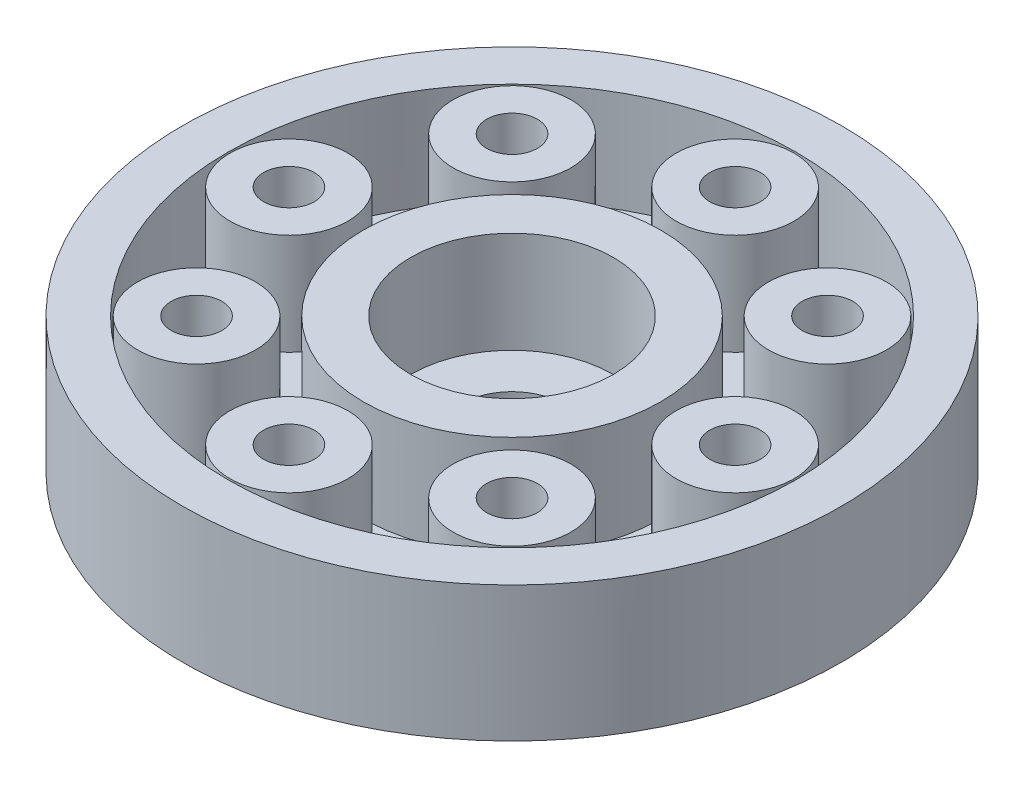
SolidWorks part; units mm, degrees
ref_plane "前视基准面" through (0, 0, 0) normal (0, 0, 1) x (1, 0, 0)
ref_plane "上视基准面" through (0, 0, 0) normal (0, 1, 0) x (1, 0, 0)
ref_plane "右视基准面" through (0, 0, 0) normal (1, 0, 0) x (0, 0, -1)
sketch "草图1" plane through (0, 0, 0) normal (0, 1, 0) x (1, 0, 0)
  circle A0 centre (0.3947, -0.592) radius 9.75
  arc A1 (-0.0261, 2.2521) -> (-0.4282, 2.7466) centre (-1.4141, 1.5344) ccw
  arc A2 (0.0949, 2.2673) -> (-0.0261, 2.2521) centre (0.3947, -0.592) ccw
  arc A3 (0.3614, 2.8463) -> (0.0949, 2.2673) centre (1.6177, 1.9174) ccw
  arc A4 (0.4279, 2.8463) -> (0.3614, 2.8463) centre (0.3947, -0.592) ccw
  arc A5 (0.6944, 2.2673) -> (0.4279, 2.8463) centre (-0.8284, 1.9174) ccw
  arc A6 (0.8154, 2.2521) -> (0.6944, 2.2673) centre (0.3947, -0.592) ccw
  arc A7 (1.2175, 2.7466) -> (0.8154, 2.2521) centre (2.2034, 1.5344) ccw
  arc A8 (1.282, 2.73) -> (1.2175, 2.7466) centre (0.3947, -0.592) ccw
  arc A9 (1.3961, 2.103) -> (1.282, 2.73) centre (-0.1659, 2.1427) ccw
  arc A10 (1.5095, 2.0581) -> (1.3961, 2.103) centre (0.3947, -0.592) ccw
  arc A11 (2.0219, 2.4371) -> (1.5095, 2.0581) centre (2.6754, 1.0178) ccw
  arc A12 (2.0803, 2.405) -> (2.0219, 2.4371) centre (0.3947, -0.592) ccw
  arc A13 (2.0348, 1.7693) -> (2.0803, 2.405) centre (0.5318, 2.1962) ccw
  arc A14 (2.1335, 1.6976) -> (2.0348, 1.7693) centre (0.3947, -0.592) ccw
  arc A15 (2.7241, 1.9372) -> (2.1335, 1.6976) centre (3.004, 0.4) ccw
  arc A16 (2.7726, 1.8917) -> (2.7241, 1.9372) centre (0.3947, -0.592) ccw
  arc A17 (2.5705, 1.2872) -> (2.7726, 1.8917) centre (1.2209, 2.0745) ccw
  arc A18 (2.6483, 1.1932) -> (2.5705, 1.2872) centre (0.3947, -0.592) ccw
  arc A19 (3.2799, 1.2785) -> (2.6483, 1.1932) centre (3.1688, -0.2801) ccw
  arc A20 (3.3156, 1.2223) -> (3.2799, 1.2785) centre (0.3947, -0.592) ccw
  arc A21 (2.9695, 0.687) -> (3.3156, 1.2223) centre (1.858, 1.7853) ccw
  arc A22 (3.0214, 0.5766) -> (2.9695, 0.687) centre (0.3947, -0.592) ccw
  arc A23 (3.6544, 0.5022) -> (3.0214, 0.5766) centre (3.1592, -0.9798) ccw
  arc A24 (3.675, 0.4389) -> (3.6544, 0.5022) centre (0.3947, -0.592) ccw
  arc A25 (3.2067, 0.0065) -> (3.675, 0.4389) centre (2.4033, 1.3467) ccw
  arc A26 (3.2295, -0.1133) -> (3.2067, 0.0065) centre (0.3947, -0.592) ccw
  arc A27 (3.8241, -0.3429) -> (3.2295, -0.1133) centre (2.9759, -1.6551) ccw
  arc A28 (3.8283, -0.4093) -> (3.8241, -0.3429) centre (0.3947, -0.592) ccw
  arc A29 (3.2672, -0.7116) -> (3.8283, -0.4093) centre (2.8223, 0.7862) ccw
  arc A30 (3.2595, -0.8334) -> (3.2672, -0.7116) centre (0.3947, -0.592) ccw
  arc A31 (3.7783, -1.2036) -> (3.2595, -0.8334) centre (2.6304, -2.2636) ccw
  arc A32 (3.7659, -1.269) -> (3.7783, -1.2036) centre (0.3947, -0.592) ccw
  arc A33 (3.1472, -1.4222) -> (3.7659, -1.269) centre (3.0888, 0.1392) ccw
  arc A34 (3.1095, -1.5382) -> (3.1472, -1.4222) centre (0.3947, -0.592) ccw
  arc A35 (3.5199, -2.0259) -> (3.1095, -1.5382) centre (2.1445, -2.7671) ccw
  arc A36 (3.4916, -2.0861) -> (3.5199, -2.0259) centre (0.3947, -0.592) ccw
  arc A37 (2.8542, -2.0806) -> (3.4916, -2.0861) centre (3.186, -0.5538) ccw
  arc A38 (2.7889, -2.1837) -> (2.8542, -2.0806) centre (0.3947, -0.592) ccw
  arc A39 (3.0652, -2.758) -> (2.7889, -2.1837) centre (1.5486, -3.1339) ccw
  arc A40 (3.0227, -2.8093) -> (3.0652, -2.758) centre (0.3947, -0.592) ccw
  arc A41 (2.4068, -2.6455) -> (3.0227, -2.8093) centre (3.1078, -1.2491) ccw
  arc A42 (2.3178, -2.7291) -> (2.4068, -2.6455) centre (0.3947, -0.592) ccw
  arc A43 (2.4426, -3.3541) -> (2.3178, -2.7291) centre (0.8801, -3.341) ccw
  arc A44 (2.3887, -3.3932) -> (2.4426, -3.3541) centre (0.3947, -0.592) ccw
  arc A45 (1.8329, -3.0814) -> (2.3887, -3.3932) centre (2.8591, -1.9032) ccw
  arc A46 (1.7259, -3.1402) -> (1.8329, -3.0814) centre (0.3947, -0.592) ccw
  arc A47 (1.6913, -3.7766) -> (1.7259, -3.1402) centre (0.1812, -3.3754) ccw
  arc A48 (1.6295, -3.8011) -> (1.6913, -3.7766) centre (0.3947, -0.592) ccw
  arc A49 (1.1686, -3.3609) -> (1.6295, -3.8011) centre (2.4556, -2.4749) ccw
  arc A50 (1.0504, -3.3912) -> (1.1686, -3.3609) centre (0.3947, -0.592) ccw
  arc A51 (0.8586, -3.999) -> (1.0504, -3.3912) centre (-0.5043, -3.2349) ccw
  arc A52 (0.7926, -4.0074) -> (0.8586, -3.999) centre (0.3947, -0.592) ccw
  arc A53 (0.4557, -3.4663) -> (0.7926, -4.0074) centre (1.9226, -2.9283) ccw
  arc A54 (0.3337, -3.4663) -> (0.4557, -3.4663) centre (0.3947, -0.592) ccw
  arc A55 (-0.0033, -4.0074) -> (0.3337, -3.4663) centre (-1.1333, -2.9283) ccw
  arc A56 (-0.0693, -3.999) -> (-0.0033, -4.0074) centre (0.3947, -0.592) ccw
  arc A57 (-0.2611, -3.3912) -> (-0.0693, -3.999) centre (1.2936, -3.2349) ccw
  arc A58 (-0.3793, -3.3609) -> (-0.2611, -3.3912) centre (0.3947, -0.592) ccw
  arc A59 (-0.8401, -3.8011) -> (-0.3793, -3.3609) centre (-1.6663, -2.4749) ccw
  arc A60 (-0.902, -3.7766) -> (-0.8401, -3.8011) centre (0.3947, -0.592) ccw
  arc A61 (-0.9366, -3.1402) -> (-0.902, -3.7766) centre (0.6081, -3.3754) ccw
  arc A62 (-1.0435, -3.0814) -> (-0.9366, -3.1402) centre (0.3947, -0.592) ccw
  arc A63 (-1.5994, -3.3932) -> (-1.0435, -3.0814) centre (-2.0698, -1.9032) ccw
  arc A64 (-1.6533, -3.3541) -> (-1.5994, -3.3932) centre (0.3947, -0.592) ccw
  arc A65 (-1.5285, -2.7291) -> (-1.6533, -3.3541) centre (-0.0908, -3.341) ccw
  arc A66 (-1.6174, -2.6455) -> (-1.5285, -2.7291) centre (0.3947, -0.592) ccw
  arc A67 (-2.2334, -2.8093) -> (-1.6174, -2.6455) centre (-2.3185, -1.2491) ccw
  arc A68 (-2.2758, -2.758) -> (-2.2334, -2.8093) centre (0.3947, -0.592) ccw
  arc A69 (-1.9995, -2.1837) -> (-2.2758, -2.758) centre (-0.7592, -3.1339) ccw
  arc A70 (-2.0649, -2.0806) -> (-1.9995, -2.1837) centre (0.3947, -0.592) ccw
  arc A71 (-2.7023, -2.0861) -> (-2.0649, -2.0806) centre (-2.3967, -0.5538) ccw
  arc A72 (-2.7306, -2.0259) -> (-2.7023, -2.0861) centre (0.3947, -0.592) ccw
  arc A73 (-2.3202, -1.5382) -> (-2.7306, -2.0259) centre (-1.3551, -2.7671) ccw
  arc A74 (-2.3579, -1.4222) -> (-2.3202, -1.5382) centre (0.3947, -0.592) ccw
  arc A75 (-2.9765, -1.269) -> (-2.3579, -1.4222) centre (-2.2995, 0.1392) ccw
  arc A76 (-2.989, -1.2036) -> (-2.9765, -1.269) centre (0.3947, -0.592) ccw
  arc A77 (-2.4702, -0.8334) -> (-2.989, -1.2036) centre (-1.8411, -2.2636) ccw
  arc A78 (-2.4779, -0.7116) -> (-2.4702, -0.8334) centre (0.3947, -0.592) ccw
  arc A79 (-3.039, -0.4093) -> (-2.4779, -0.7116) centre (-2.033, 0.7862) ccw
  arc A80 (-3.0348, -0.3429) -> (-3.039, -0.4093) centre (0.3947, -0.592) ccw
  arc A81 (-2.4402, -0.1133) -> (-3.0348, -0.3429) centre (-2.1866, -1.6551) ccw
  arc A82 (-2.4173, 0.0065) -> (-2.4402, -0.1133) centre (0.3947, -0.592) ccw
  arc A83 (-2.8857, 0.4389) -> (-2.4173, 0.0065) centre (-1.6139, 1.3467) ccw
  arc A84 (-2.8651, 0.5022) -> (-2.8857, 0.4389) centre (0.3947, -0.592) ccw
  arc A85 (-2.2321, 0.5766) -> (-2.8651, 0.5022) centre (-2.3699, -0.9798) ccw
  arc A86 (-2.1802, 0.687) -> (-2.2321, 0.5766) centre (0.3947, -0.592) ccw
  arc A87 (-2.5263, 1.2223) -> (-2.1802, 0.687) centre (-1.0687, 1.7853) ccw
  arc A88 (-2.4906, 1.2785) -> (-2.5263, 1.2223) centre (0.3947, -0.592) ccw
  arc A89 (-1.859, 1.1932) -> (-2.4906, 1.2785) centre (-2.3794, -0.2801) ccw
  arc A90 (-1.7812, 1.2872) -> (-1.859, 1.1932) centre (0.3947, -0.592) ccw
  arc A91 (-1.9833, 1.8917) -> (-1.7812, 1.2872) centre (-0.4315, 2.0745) ccw
  arc A92 (-1.9348, 1.9372) -> (-1.9833, 1.8917) centre (0.3947, -0.592) ccw
  arc A93 (-1.3442, 1.6976) -> (-1.9348, 1.9372) centre (-2.2147, 0.4) ccw
  arc A94 (-1.2455, 1.7693) -> (-1.3442, 1.6976) centre (0.3947, -0.592) ccw
  arc A95 (-1.2909, 2.405) -> (-1.2455, 1.7693) centre (0.2576, 2.1962) ccw
  arc A96 (-1.2326, 2.4371) -> (-1.2909, 2.405) centre (0.3947, -0.592) ccw
  arc A97 (-0.7202, 2.0581) -> (-1.2326, 2.4371) centre (-1.886, 1.0178) ccw
  arc A98 (-0.6067, 2.103) -> (-0.7202, 2.0581) centre (0.3947, -0.592) ccw
  arc A99 (-0.4927, 2.73) -> (-0.6067, 2.103) centre (0.9553, 2.1427) ccw
  arc A100 (-0.4282, 2.7466) -> (-0.4927, 2.73) centre (0.3947, -0.592) ccw
extrude "凸台-拉伸1" add sketch "草图1" along normal blind 3
ref_plane "基准面1" through (0, 0, 0) normal (0, -1, 0) x (-1, 0, 0)
sketch "草图2" plane through (0, 0, 0) normal (0, -1, 0) x (-1, 0, 0)
  line L0 (10.4941, -0.7442) -> (4.2859, -0.7442) construction
  circle A0 centre (-0.3947, -0.592) radius 9.75
extrude "凸台-拉伸2" add sketch "草图2" along normal blind 1
ref_plane "基准面2" through (0, 0, 0) normal (0, 1, 0) x (1, 0, 0)
sketch "草图4" plane through (0, 0, 0) normal (0, 1, 0) x (1, 0, 0)
  circle A0 centre (0.3947, -0.592) radius 1.5
extrude "切除-拉伸4" cut sketch "草图4" against normal blind 1
ref_plane "基准面3" through (0, 3, 0) normal (0, 1, 0) x (1, 0, 0)
sketch "草图5" plane through (0, 0, 0) normal (0, -1, 0) x (-1, 0, 0)
  circle A0 centre (-0.3947, -0.592) radius 4.4
  circle A1 centre (-0.3947, -0.592) radius 8.4
extrude "切除-拉伸5" cut sketch "草图5" against normal blind 10
sketch "草图6" plane through (0, 0, 0) normal (0, -1, 0) x (-1, 0, 0)
  line L0 (-0.3947, -0.592) -> (-0.3947, 7.808) construction
  circle A0 centre (-0.3947, -0.592) radius 6.6 construction
  circle A1 centre (-0.3947, -0.592) radius 8.4 construction
  circle A2 centre (-0.3947, 6.008) radius 0.75
  circle A3 centre (4.2722, 4.0749) radius 0.75
  circle A4 centre (6.2053, -0.592) radius 0.75
  circle A5 centre (4.2722, -5.2589) radius 0.75
  circle A6 centre (-0.3947, -7.192) radius 0.75
  circle A7 centre (-5.0616, -5.2589) radius 0.75
  circle A8 centre (-6.9947, -0.592) radius 0.75
  circle A9 centre (-5.0616, 4.0749) radius 0.75
  circle A10 centre (-0.3947, 6.008) radius 1.7445
  circle A11 centre (4.2722, 4.0749) radius 1.7445
  circle A12 centre (6.2053, -0.592) radius 1.7445
  circle A13 centre (4.2722, -5.2589) radius 1.7445
  circle A14 centre (-0.3947, -7.192) radius 1.7445
  circle A15 centre (-5.0616, -5.2589) radius 1.7445
  circle A16 centre (-6.9947, -0.592) radius 1.7445
  circle A17 centre (-5.0616, 4.0749) radius 1.7445
  point P26 (-0.3947, -0.592)
  point P42 (-0.3947, -0.592)
  dimension "D1" = 8
  dimension "D2" = 8
extrude "凸台-拉伸3" add sketch "草图6" against normal blind 3
ref_plane "基准面4" through (0, -1, 0) normal (0, -1, 0) x (-1, 0, 0)
sketch "草图7" plane through (0, -1, 0) normal (0, -1, 0) x (-1, 0, 0)
  circle A0 centre (-0.3947, 6.008) radius 0.75 construction
  circle A1 centre (-0.3947, -0.592) radius 1.5 construction
  circle A2 centre (-0.3947, 6.008) radius 0.75
  circle A3 centre (-0.3947, -0.592) radius 1.5
  circle A4 centre (4.2722, 4.0749) radius 0.75
  circle A5 centre (6.2053, -0.592) radius 0.75
  circle A6 centre (4.2722, -5.2589) radius 0.75
  circle A7 centre (-0.3947, -7.192) radius 0.75
  circle A8 centre (-5.0616, -5.2589) radius 0.75
  circle A9 centre (-6.9947, -0.592) radius 0.75
  circle A10 centre (-5.0616, 4.0749) radius 0.75
  point P23 (0, 0)
  point P24 (-0.3947, -0.592)
  dimension "D1" = 8
extrude "切除-拉伸6" cut sketch "草图7" against normal blind 3
ref_plane "基准面5" through (0, 3, 0) normal (0, 1, 0) x (1, 0, 0)
sketch "草图8" plane through (0, 3, 0) normal (0, 1, 0) x (1, 0, 0)
  circle A0 centre (0.3947, -0.592) radius 4
extrude "切除-拉伸7" cut sketch "草图8" against normal blind 3
ref_plane "基准面6" through (0, 0, 0) normal (0, 1, 0) x (1, 0, 0)
sketch "草图9" plane through (0, 0, 0) normal (0, 1, 0) x (1, 0, 0)
  circle A0 centre (0.3947, -0.592) radius 4
  circle A1 centre (0.3947, -0.592) radius 3
extrude "凸台-拉伸4" add sketch "草图9" along normal blind 3
